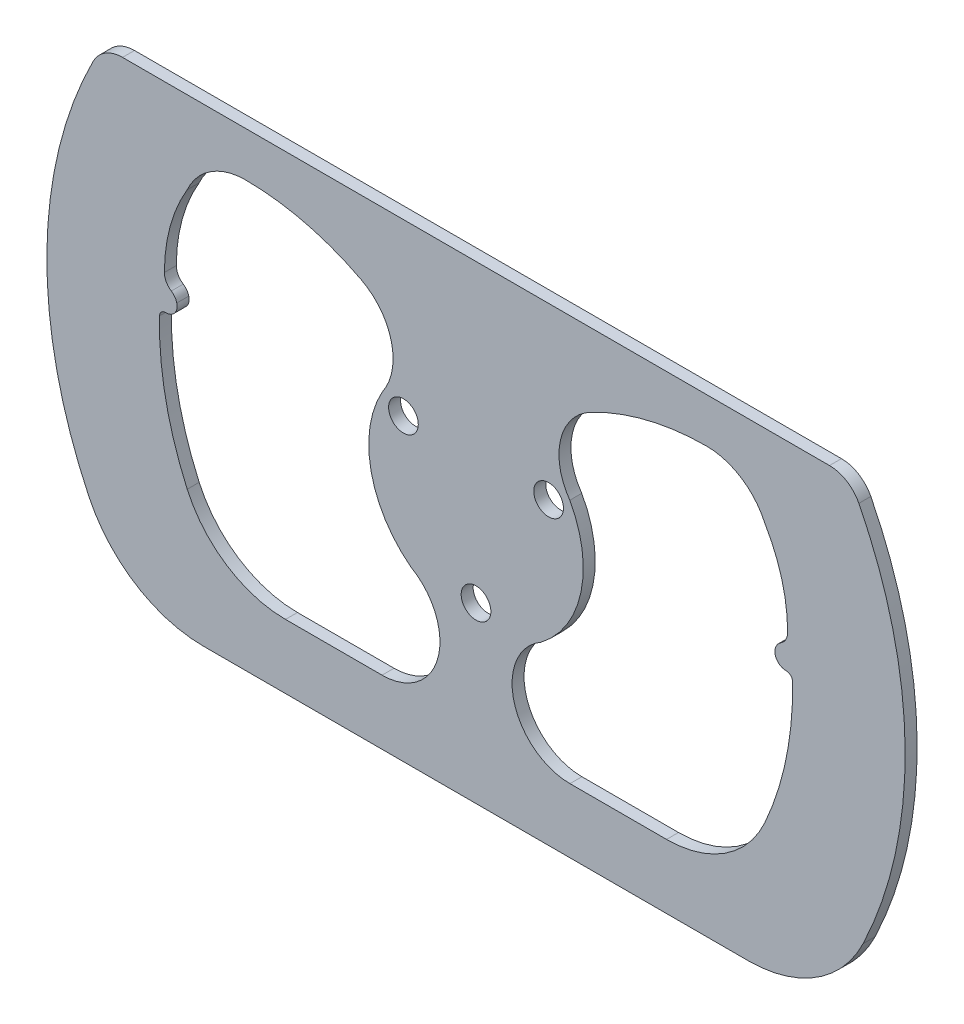
SolidWorks part; units mm, degrees
ref_plane "Front Plane" through (0, 0, 0) normal (0, 0, 1) x (1, 0, 0)
ref_plane "Top Plane" through (0, 0, 0) normal (0, 1, 0) x (1, 0, 0)
ref_plane "Right Plane" through (0, 0, 0) normal (1, 0, 0) x (0, 0, -1)
sketch "Sketch1" plane through (0, 0, 0) normal (0, 0, 1) x (1, 0, 0)
  line L0 (-19.2532, 11.1158) -> (19.2532, 11.1158) construction
  line L1 (19.2532, 11.1158) -> (0, -22.2317) construction
  line L2 (0, -22.2317) -> (-19.2532, 11.1158) construction
  line L3 (-19.2532, 11.1158) -> (0, 0) construction
  line L4 (0, 0) -> (19.2532, 11.1158) construction
  line L7 (93.7554, 56.2179) -> (-93.7554, 56.2179)
  line L42 (72.259, -68.3114) -> (-72.259, -68.3114)
  line L43 (113.8304, 0) -> (-113.8304, 0) construction
  line L44 (113.8304, 0) -> (83.9738, 0)
  line L45 (0, 0) -> (0, 56.2179) construction
  line L46 (50.5376, -51.2718) -> (24.9214, -51.2718)
  line L47 (-50.5376, -51.2718) -> (-24.9214, -51.2718)
  circle A5 centre (0, 0) radius 28.448 construction
  arc A10 (102.6706, -49.1539) -> (101.5508, 51.4276) centre (0, 0) ccw
  arc A11 (93.7554, 56.2179) -> (101.5508, 51.4276) centre (93.7554, 47.4798) cw
  arc A12 (-93.7554, 56.2179) -> (-101.5508, 51.4276) centre (-93.7554, 47.4798) ccw
  arc A40 (-102.6706, -49.1539) -> (-72.259, -68.3114) centre (-72.259, -34.5943) ccw
  arc A90 (102.6706, -49.1539) -> (72.259, -68.3114) centre (72.259, -34.5943) cw
  arc A91 (-102.6706, -49.1539) -> (-101.5508, 51.4276) centre (0, 0) cw
  arc A93 (76.6017, 34.4062) -> (61.1114, 44.3865) centre (61.1779, 27.4784) ccw
  arc A94 (76.6017, -34.4062) -> (50.5376, -51.2718) centre (50.5376, -22.6993) cw
  arc A95 (24.9214, -51.2718) -> (17.2622, -22.612) centre (24.9214, -35.9185) cw
  arc A96 (61.1114, 44.3865) -> (30.4385, 36.7991) centre (61.3741, -22.4684) ccw
  arc A97 (30.4385, 36.7991) -> (24.8687, 13.8144) centre (37.709, 22.8701) ccw
  arc A98 (24.8687, 13.8144) -> (17.2622, -22.612) centre (0, 0) cw
  arc A99 (-30.4385, 36.7991) -> (-24.8687, 13.8144) centre (-37.709, 22.8701) cw
  arc A100 (-61.1114, 44.3865) -> (-30.4385, 36.7991) centre (-61.3741, -22.4684) cw
  arc A101 (-76.6017, 34.4062) -> (-61.1114, 44.3865) centre (-61.1779, 27.4784) cw
  arc A103 (-76.6017, -34.4062) -> (-50.5376, -51.2718) centre (-50.5376, -22.6993) ccw
  arc A104 (-24.9214, -51.2718) -> (-17.2622, -22.612) centre (-24.9214, -35.9185) ccw
  arc A105 (-24.8687, 13.8144) -> (-17.2622, -22.612) centre (0, 0) ccw
  circle A106 centre (0, -22.2317) radius 3.937
  circle A107 centre (-19.2532, 11.1158) radius 3.937
  circle A108 centre (19.2532, 11.1158) radius 3.937
  arc A109 (76.6017, -34.4062) -> (83.9563, 1.7175) centre (0, 0) ccw
  arc A110 (83.9563, 1.7175) -> (82.2858, 3.3211) centre (82.3193, 1.684) ccw
  arc A111 (82.2858, 3.3211) -> (79.3667, 6.9896) centre (82.2255, 6.2687) cw
  arc A112 (79.3667, 6.9896) -> (80.8267, 9.0174) centre (82.6574, 6.1598) cw
  arc A113 (80.8267, 9.0174) -> (82.6574, 12.3644) centre (78.6825, 12.3644) ccw
  arc A114 (82.6574, 12.3644) -> (76.6017, 34.4062) centre (39.5149, 12.3644) ccw
  arc A115 (-83.9563, 1.7175) -> (-82.2858, 3.3211) centre (-82.3193, 1.684) cw
  arc A116 (-80.8267, 9.0174) -> (-82.6574, 12.3644) centre (-78.6825, 12.3644) cw
  arc A117 (-79.3667, 6.9896) -> (-80.8267, 9.0174) centre (-82.6574, 6.1598) ccw
  arc A118 (-82.2858, 3.3211) -> (-79.3667, 6.9896) centre (-82.2255, 6.2687) ccw
  arc A119 (-76.6017, -34.4062) -> (-83.9563, 1.7175) centre (0, 0) cw
  arc A120 (-82.6574, 12.3644) -> (-76.6017, 34.4062) centre (-39.5149, 12.3644) cw
  point P12 (0, 56.2179)
  point P17 (0, 56.2179)
  point P20 (0, -68.3114)
  point P59 (0, 51.7389)
  point P74 (0, 51.7389)
  point P77 (0, 51.7389)
  point P78 (0, 51.7389)
  point P83 (0, 28.448)
  dimension "D9" = 56.896
  dimension "D3" = 38.5064
extrude "Boss-Extrude1" add sketch "Sketch1" along normal blind 3.175
